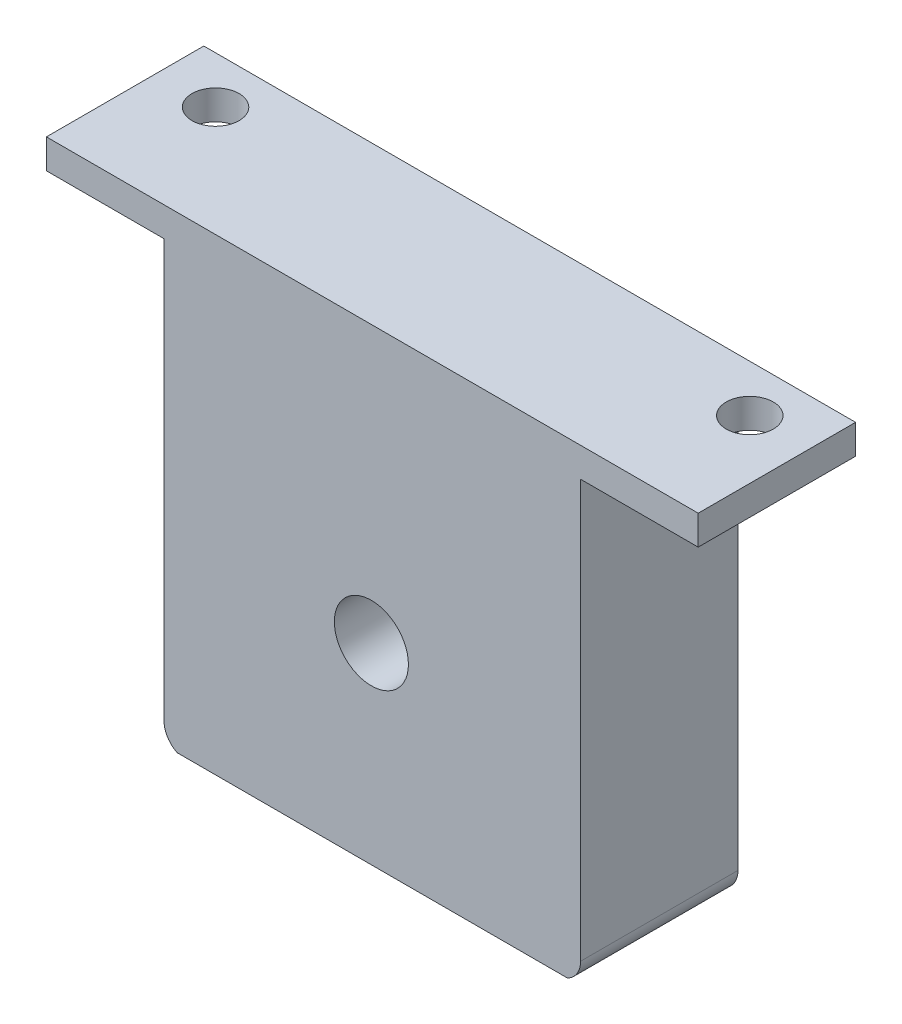
SolidWorks part; units mm, degrees
ref_plane "Front Plane" through (0, 0, 0) normal (0, 0, 1) x (1, 0, 0)
ref_plane "Top Plane" through (0, 0, 0) normal (0, 1, 0) x (1, 0, 0)
ref_plane "Right Plane" through (0, 0, 0) normal (1, 0, 0) x (0, 0, -1)
sketch "Sketch1" plane through (0, 0, 0) normal (0, 0, 1) x (1, 0, 0)
  line L1 (0, 0) -> (45, 0)
  line L2 (0, 0) -> (0, 50.8)
  line L3 (0, 50.8) -> (45, 50.8)
  line L4 (45, 0) -> (45, 50.8)
  circle A0 centre (22.4, 21) radius 4
  dimension "D3" = 8
  dimension "D1" = 45
  dimension "D2" = 50.8
  dimension "D4" = 21
  dimension "D5" = 22.4
extrude "Boss-Extrude1" add sketch "Sketch1" along normal blind 17
fillet "Fillet1" radius 2.54 2 edges at (0, 0, 8.5) (45, 0, 8.5)
sketch "Sketch3" plane through (45, 0, 0) normal (1, 0, 0) x (0, 0, -1)
  line L0 (-17, 2.54) -> (-17, 50.8) construction
  line L1 (0, 0) -> (-17, 0)
  line L2 (0, 0) -> (0, 0.254)
  line L3 (0, 0.254) -> (-17, 0.254)
  line L4 (-17, 0) -> (-17, 0.254)
  dimension "D1" = 0.254
extrude "Cut-Extrude2" cut sketch "Sketch3" against normal through all
sketch "Sketch4" plane through (0, 50.8, 0) normal (0, 1, 0) x (1, 0, 0)
  line L0 (45, -17) -> (0, -17) construction
  line L1 (45, 0) -> (57.7, 0)
  line L2 (45, 0) -> (45, -17)
  line L3 (45, -17) -> (57.7, -17)
  line L4 (57.7, 0) -> (57.7, -17)
  line L5 (45, 0) -> (57.7, -17) construction
  line L6 (45, -17) -> (57.7, 0) construction
  line L7 (0, 0) -> (-12.7, 0)
  line L8 (0, 0) -> (0, -17)
  line L9 (0, -17) -> (-12.7, -17)
  line L10 (-12.7, 0) -> (-12.7, -17)
  line L11 (0, 0) -> (-12.7, -17) construction
  line L12 (0, -17) -> (-12.7, 0) construction
  circle A2 centre (-6.35, -5.08) radius 2.54
  circle A3 centre (51.35, -5.08) radius 2.54
  point P4 (51.35, -8.5)
  point P10 (-6.35, -8.5)
  dimension "D5" = 5.08
  dimension "D6" = 5.08
  dimension "D7" = 5.08
  dimension "D1" = 0
  dimension "D2" = 0
  dimension "D3" = 12.7
  dimension "D4" = 12.7
  dimension "D8" = 5.08
extrude "Boss-Extrude2" add sketch "Sketch4" against normal blind 3.175
